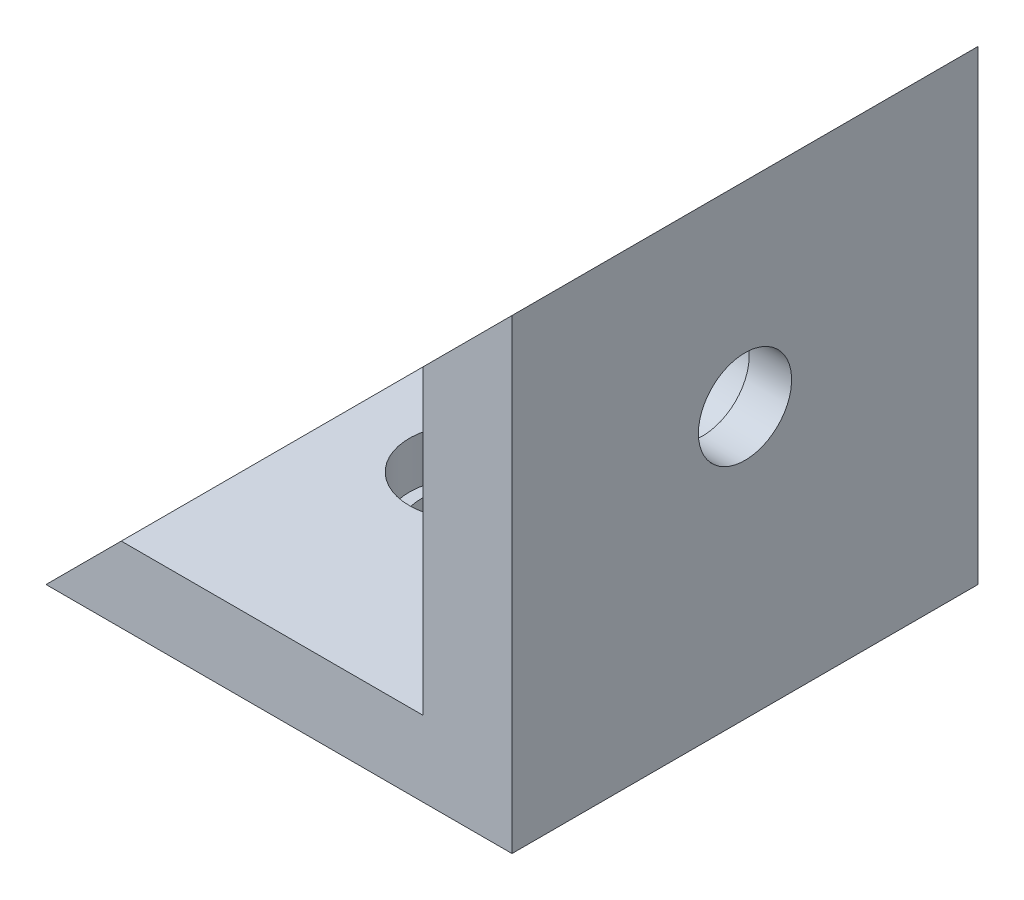
SolidWorks part; units mm, degrees
ref_plane "Front Plane" through (0, 0, 0) normal (0, 0, 1) x (1, 0, 0)
ref_plane "Top Plane" through (0, 0, 0) normal (0, 1, 0) x (1, 0, 0)
ref_plane "Right Plane" through (0, 0, 0) normal (1, 0, 0) x (0, 0, -1)
sketch "Çizim1" plane through (0, 0, 0) normal (0, 0, 1) x (1, 0, 0)
  line L1 (-23.1728, -15.6221) -> (-3.1728, -15.6221)
  line L2 (-23.1728, -15.6221) -> (-23.1728, 4.3779)
  line L3 (-23.1728, 4.3779) -> (-3.1728, 4.3779)
  line L4 (-3.1728, -15.6221) -> (-3.1728, 4.3779)
extrude "Yükseklik-Ekstrüzyon1" add sketch "Çizim1" along normal blind 20 contours L2 L1 L4 L3
sketch "Çizim2" plane through (0, 0, 20) normal (0, 0, 1) x (1, 0, 0)
  line L0 (-3.1728, 4.3779) -> (-23.1728, -15.6221)
  line L1 (-23.1728, -15.6221) -> (-23.1728, 4.3779)
  line L2 (-23.1728, 4.3779) -> (-3.1728, 4.3779)
extrude "Kes-Ekstrüzyon1" cut sketch "Çizim2" against normal blind 20
sketch "Çizim3" plane through (0, 0, 20) normal (0, 0, 1) x (1, 0, 0)
  line L2 (-6.9894, -12.392) -> (-24.214, -12.392)
  line L3 (-6.9894, -12.392) -> (-6.9894, 4.8564)
  line L4 (-6.9894, 4.8564) -> (-24.214, 4.8564)
  line L5 (-24.214, -12.392) -> (-24.214, 4.8564)
extrude "Kes-Ekstrüzyon2" cut sketch "Çizim3" against normal blind 20 contours L3 L2 L5 L4
sketch "Çizim4" plane through (-6.9894, 0, 0) normal (-1, 0, 0) x (0, 0, 1)
  line L0 (0, 4.3779) -> (20, -12.392) construction
  circle A0 centre (10, -4.007) radius 2
extrude "Kes-Ekstrüzyon3" cut sketch "Çizim4" against normal blind 20
sketch "Çizim7" plane through (-6.9894, 0, 0) normal (-1, 0, 0) x (0, 0, 1)
  circle A0 centre (10, -4.007) radius 2.5
extrude "Kes-Ekstrüzyon7" cut sketch "Çizim7" against normal blind 2
sketch "Çizim8" plane through (0, -12.392, 0) normal (0, 1, 0) x (1, 0, 0)
  line L0 (-23.1728, 0) -> (-6.9894, -20) construction
  circle A0 centre (-15.0811, -10) radius 2
extrude "Kes-Ekstrüzyon8" cut sketch "Çizim8" against normal blind 10
sketch "Çizim9" plane through (0, -12.392, 0) normal (0, 1, 0) x (1, 0, 0)
  circle A0 centre (-15.0811, -10) radius 2.5
extrude "Kes-Ekstrüzyon9" cut sketch "Çizim9" against normal blind 2
